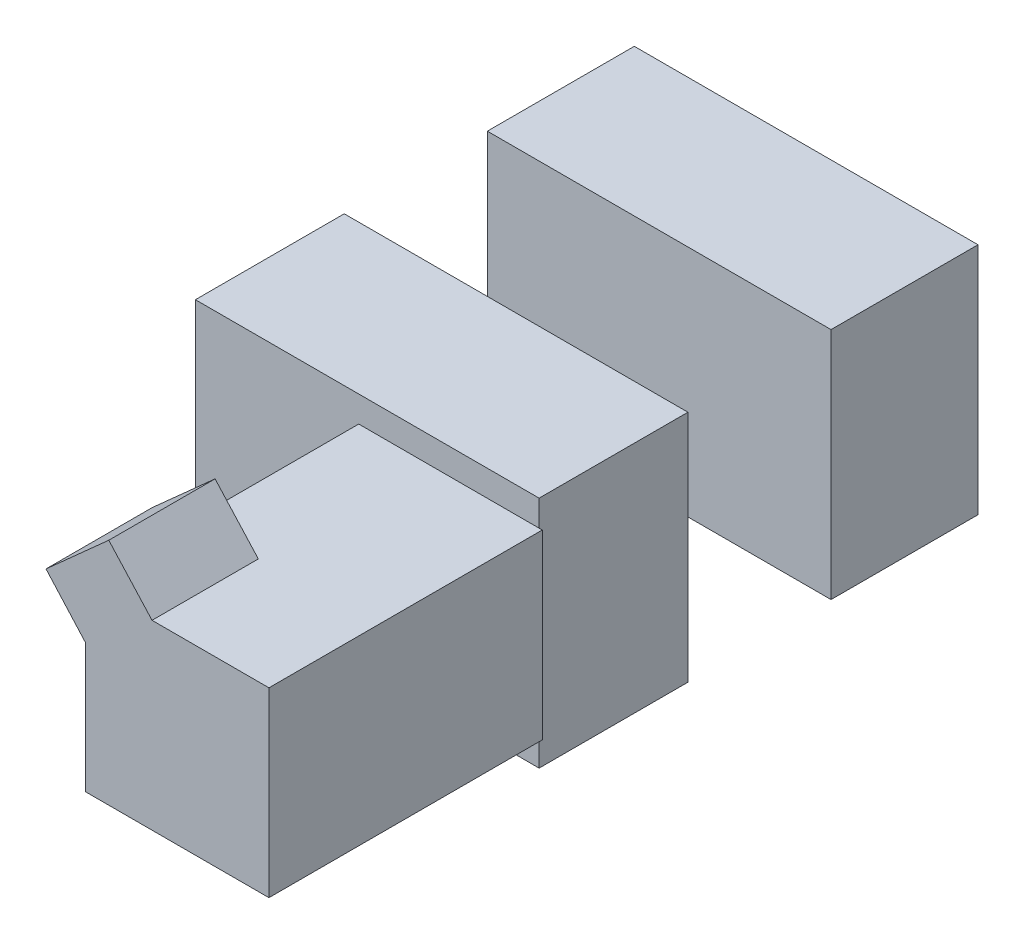
SolidWorks part; units mm, degrees
ref_plane "Front Plane" through (0, 0, 0) normal (0, 0, 1) x (1, 0, 0)
ref_plane "Top Plane" through (0, 0, 0) normal (0, 1, 0) x (1, 0, 0)
ref_plane "Right Plane" through (0, 0, 0) normal (1, 0, 0) x (0, 0, -1)
other "Graphic1"
sketch "Sketch1" plane through (0, 0, 0) normal (0, 1, 0) x (1, 0, 0)
  line L1 (-0.084, 0.0721) -> (0.0292, 0.0721)
  line L2 (-0.084, 0.0721) -> (-0.084, 0.0237)
  line L3 (-0.084, 0.0237) -> (0.0292, 0.0237)
  line L4 (0.0292, 0.0721) -> (0.0292, 0.0237)
  line L5 (0.0292, -0.0724) -> (-0.084, -0.0724)
  line L6 (0.0292, -0.0724) -> (0.0292, -0.0234)
  line L7 (0.0292, -0.0234) -> (-0.084, -0.0234)
  line L8 (-0.084, -0.0724) -> (-0.084, -0.0234)
  dimension "D1" = 0.0237
  dimension "D2" = 0.1132
  dimension "D3" = 0.0484
  dimension "D4" = 0.049
  dimension "D5" = 0.1132
  dimension "D6" = 0.0234
  dimension "D7" = 0.0292
  dimension "D8" = 0.0292
extrude "Boss-Extrude1" add sketch "Sketch1" along normal mid plane 0.077
sketch "Sketch2" plane through (0, 0, 0.0724) normal (0, 0, 1) x (1, 0, 0)
  line L0 (0, 0) -> (0.0302, 0) construction
  line L1 (0.0302, 0) -> (0.0302, 0.0328) construction
  line L2 (0.0302, 0.0299) -> (0, 0.0299) construction
  line L4 (-0.0302, -0.0299) -> (0.0302, -0.0299)
  line L5 (-0.0302, -0.0299) -> (-0.0302, 0.0299)
  line L6 (-0.0302, 0.0299) -> (0.0302, 0.0299)
  line L7 (0.0302, -0.0299) -> (0.0302, 0.0299)
  line L8 (-0.0302, -0.0299) -> (0.0302, 0.0299) construction
  line L9 (-0.0302, 0.0299) -> (0.0302, -0.0299) construction
extrude "Boss-Extrude2" add sketch "Sketch2" along normal blind 0.09
sketch "Sketch3" plane through (0, 0, 0.1624) normal (0, 0, 1) x (1, 0, 0)
  line L0 (-0.0302, 0.0126) -> (-0.0432, 0.0271)
  line L1 (-0.0302, 0.0299) -> (-0.0302, -0.0299) construction
  line L2 (-0.0432, 0.0271) -> (-0.0225, 0.0456)
  line L3 (-0.0225, 0.0456) -> (-0.0079, 0.0295)
  line L4 (-0.0079, 0.0295) -> (-0.0302, 0.0126)
extrude "Boss-Extrude3" add sketch "Sketch3" against normal blind 0.035
